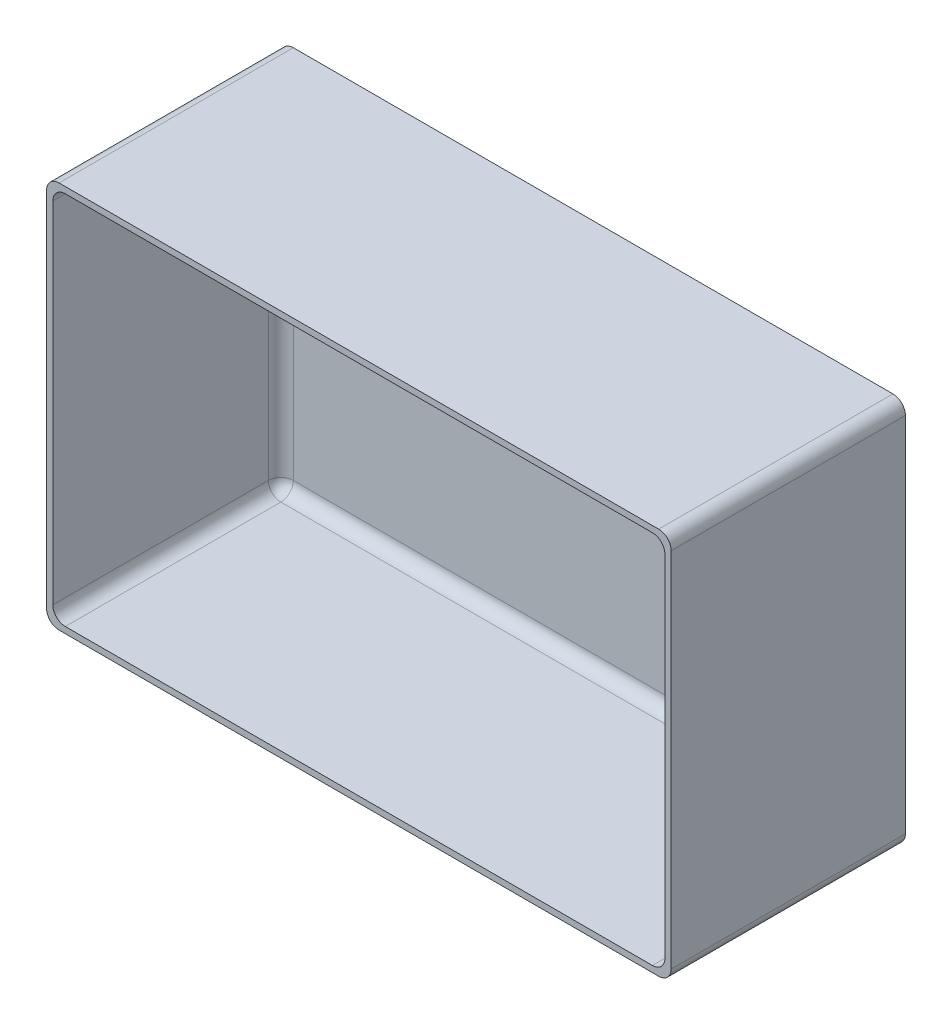
SolidWorks part; units mm, degrees
ref_plane "Plan de face" through (0, 0, 0) normal (0, 0, 1) x (1, 0, 0)
ref_plane "Plan de dessus" through (0, 0, 0) normal (0, 1, 0) x (1, 0, 0)
ref_plane "Plan de droite" through (0, 0, 0) normal (1, 0, 0) x (0, 0, -1)
sketch "Esquisse1" plane through (0, 0, 0) normal (0, 0, 1) x (1, 0, 0)
  line L1 (-40, 24.8) -> (40, 24.8)
  line L2 (-40, 24.8) -> (-40, -24.8)
  line L3 (-40, -24.8) -> (40, -24.8)
  line L4 (40, 24.8) -> (40, -24.8)
  line L5 (-40, 24.8) -> (40, -24.8) construction
  line L6 (-40, -24.8) -> (40, 24.8) construction
  point P0 (0, 0)
  dimension "D1" = 80
  dimension "D2" = 49.6
extrude "Boss.-Extru.1" add sketch "Esquisse1" along normal blind 30
shell "Coque1" thickness 0.8
fillet "Congé1" radius 1.6 12 edges at (39.2, 0, 0.8) (-39.2, 0, 0.8) (0, -24, 0.8) (39.2, -24, 15.4) (-39.2, -24, 15.4) (39.2, 24, 15.4) (0, 24, 0.8) (-39.2, 24, 15.4) (40, -24.8, 15) (-40, 24.8, 15) (40, 24.8, 15) (-40, -24.8, 15)
